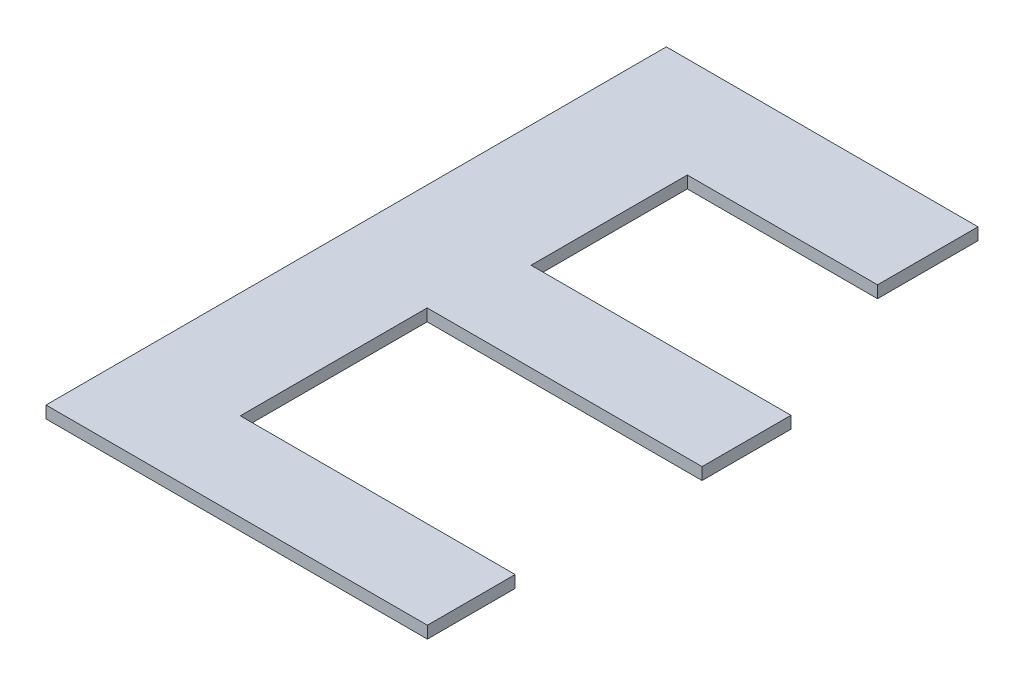
SolidWorks part; units mm, degrees
ref_plane "Plano frontal" through (0, 0, 0) normal (0, 0, 1) x (1, 0, 0)
ref_plane "Plano superior" through (0, 0, 0) normal (0, 1, 0) x (1, 0, 0)
ref_plane "Plano direito" through (0, 0, 0) normal (1, 0, 0) x (0, 0, -1)
sketch3d "3DSketch1"
  line L0 (-22850.5611, 6426.0932, 40322.6002) -> (-23117.9925, 6426.0932, 40322.6002) construction
  line L1 (-22850.5611, 4903.7221, 40322.6002) -> (-22850.5611, 6715.4106, 40322.6002) construction
  line L2 (-23117.9925, 6426.0932, 40322.6002) -> (-23117.9925, 6426.0932, 40992.8389) construction
  line L3 (-23117.9925, 6426.0932, 40992.8389) -> (-22583.1297, 6426.0932, 40992.8389) construction
  line L4 (-22583.1297, 6426.0932, 40992.8389) -> (-22583.1297, 6426.0932, 40322.6002) construction
  line L5 (-22583.1297, 6426.0932, 40322.6002) -> (-22850.5611, 6426.0932, 40322.6002) construction
  line L7 (-22583.1297, 6426.0932, 40992.8389) -> (-22583.1297, 6426.0932, 40322.6002)
  line L8 (-22583.1297, 6426.0932, 40992.8389) -> (-23117.9925, 6426.0932, 40992.8389)
  line L9 (-23117.9925, 6426.0932, 40992.8389) -> (-23117.9925, 6426.0932, 40322.6002)
  line L10 (-22583.1297, 6426.0932, 40322.6002) -> (-23117.9925, 6426.0932, 40322.6002)
ref_plane "Plane1" through (0, 6237.8571, 0) normal (0, -1, 0) x (-1, 0, 0)
sketch "Sketch1" plane through (0, 6237.8571, 0) normal (0, -1, 0) x (-1, 0, 0)
  line L1 (22922.5806, -40965.3532) -> (23295.7006, -40965.3532)
  line L2 (22922.5806, -40965.3532) -> (22922.5806, -40110.1117)
  line L3 (22922.5806, -40110.1117) -> (23295.7006, -40110.1117)
  line L4 (23295.7006, -40965.3532) -> (23295.7006, -40110.1117)
sketch "Sketch2" plane through (0, 6587.8571, 0) normal (0, -1, 0) x (1, 0, 0)
  line L2 (-23417.7711, 41050.1414) -> (-23417.7711, 40189.1002)
  line L3 (-23216.6143, 40189.1002) -> (-22901.5611, 40189.1002)
  line L5 (-22901.5611, 40189.1002) -> (-22901.5611, 40022.6805)
  line L6 (-22901.5611, 40022.6805) -> (-23417.7711, 40022.6805)
  line L7 (-23417.7711, 40022.6805) -> (-23417.7711, 40189.1002)
  line L8 (-22901.5611, 40189.1002) -> (-22901.5611, 40199.9002) construction
  line L9 (-23216.6143, 40189.1002) -> (-23216.6143, 40447.9248)
  line L10 (-23216.6143, 40447.9248) -> (-22786.0831, 40447.9248)
  line L11 (-22786.0831, 40447.9248) -> (-22786.0831, 40595.178)
  line L12 (-22786.0831, 40595.178) -> (-23241.3811, 40595.178)
  line L13 (-23241.3811, 40595.178) -> (-23241.3811, 40904.7371)
  line L14 (-23241.3811, 40904.7371) -> (-22786.0831, 40904.7371)
  line L15 (-22786.0831, 40904.7371) -> (-22786.0831, 41050.1414)
  line L16 (-22786.0831, 41050.1414) -> (-23417.7711, 41050.1414)
extrude "Boss-Extrude1" add sketch "Sketch2" along normal blind 20 from offset 500
sketch3d "3DSketch2"
  line L0 (-23417.7711, 6087.8571, 40022.6805) -> (-23417.7711, 6283.6368, 40208.0733)
  line L1 (-23417.7711, 6087.8571, 41050.1414) -> (-23417.7711, 6087.8571, 40022.6805) construction
  line L2 (-23417.7711, 6283.6368, 40208.0733) -> (-23417.7711, 6254.5494, 40208.0733)
  line L3 (-23417.7711, 6087.8571, 40208.0733) -> (-23417.7711, 6087.8571, 40022.6805)
  line L4 (-23417.7711, 6254.5494, 40208.0733) -> (-23417.7711, 6107.8571, 40069.1636)
  line L5 (-23417.7711, 6107.8571, 40069.1636) -> (-23417.7711, 6107.8571, 40208.0733)
  line L6 (-23417.7711, 6107.8571, 40208.0733) -> (-23417.7711, 6087.8571, 40208.0733)
  dimension "D1" = 20
  dimension "D2" = 20
